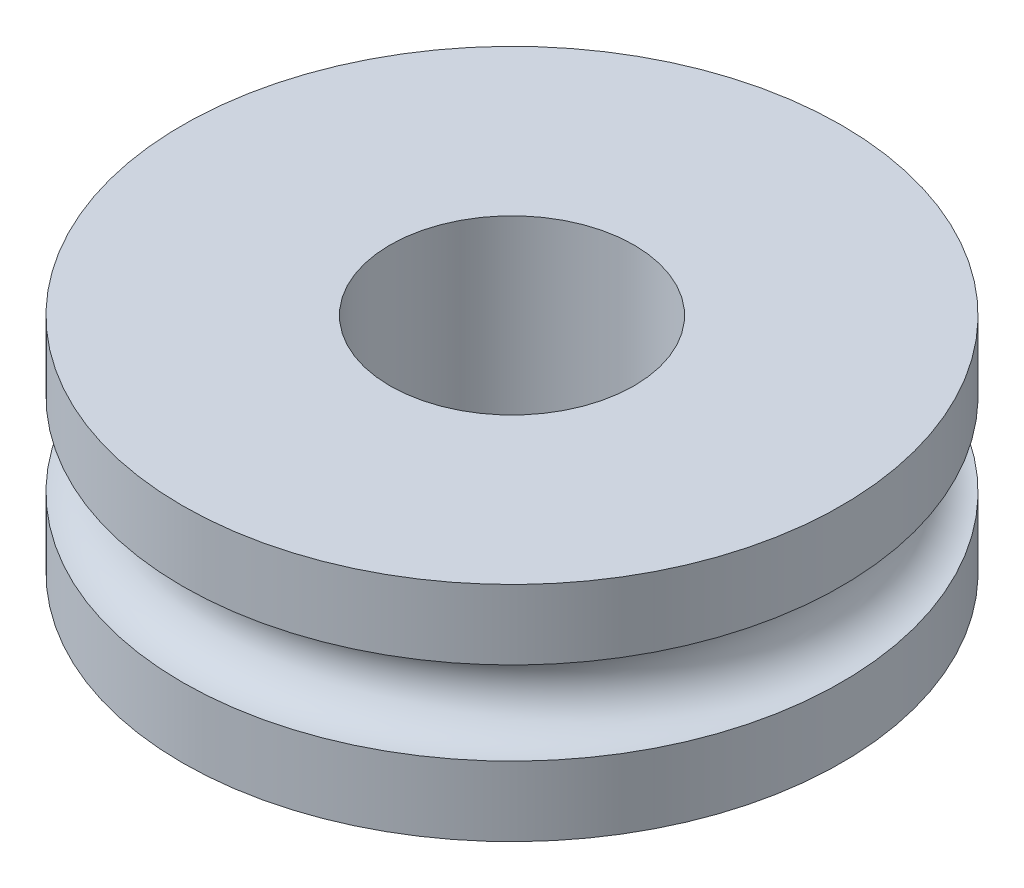
SolidWorks part; units mm, degrees
ref_plane "前视基准面" through (0, 0, 0) normal (0, 0, 1) x (1, 0, 0)
ref_plane "上视基准面" through (0, 0, 0) normal (0, 1, 0) x (1, 0, 0)
ref_plane "右视基准面" through (0, 0, 0) normal (1, 0, 0) x (0, 0, -1)
sketch "Sketch1" plane through (0, 0, 0) normal (0, 0, 1) x (1, 0, 0)
  line L0 (0, 0) -> (0, 51.4164) construction
  line L2 (-28.1754, 0) -> (-76.0842, 0)
  line L3 (-28.1754, 0) -> (-28.1754, 51.4164)
  line L4 (-28.1754, 51.4164) -> (-76.0842, 51.4164)
  line L5 (-76.0842, 0) -> (-76.0842, 51.4164)
revolve "Revolve1" add sketch "Sketch1" angle 360 about L0
sketch "Sketch3" plane through (0, 0, 0) normal (0, 0, 1) x (1, 0, 0)
  line L0 (0, 0) -> (0, 51.4164) construction
  line L1 (76.0842, 51.4164) -> (-76.0842, 51.4164) construction
  line L2 (-76.0842, 51.4164) -> (-76.0842, 0) construction
  circle A0 centre (-76.0842, 25.7082) radius 9.6089
revolve "Cut-Revolve1" cut sketch "Sketch3" angle 360 about L0
